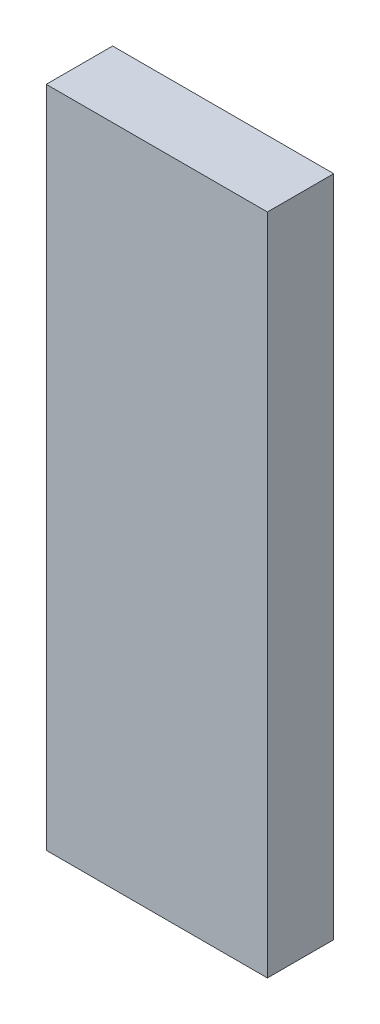
SolidWorks part; units mm, degrees
ref_plane "Front Plane" through (0, 0, 0) normal (0, 0, 1) x (1, 0, 0)
ref_plane "Top Plane" through (0, 0, 0) normal (0, 1, 0) x (1, 0, 0)
ref_plane "Right Plane" through (0, 0, 0) normal (1, 0, 0) x (0, 0, -1)
sketch "Sketch2" plane through (0, 0, 0) normal (0, 1, 0) x (1, 0, 0)
  line L1 (-5, 1.5) -> (5, 1.5)
  line L2 (-5, 1.5) -> (-5, -1.5)
  line L3 (-5, -1.5) -> (5, -1.5)
  line L4 (5, 1.5) -> (5, -1.5)
  line L5 (-5, 1.5) -> (5, -1.5) construction
  line L6 (-5, -1.5) -> (5, 1.5) construction
  point P0 (0, 0)
extrude "Boss-Extrude1" add sketch "Sketch2" along normal blind 30
